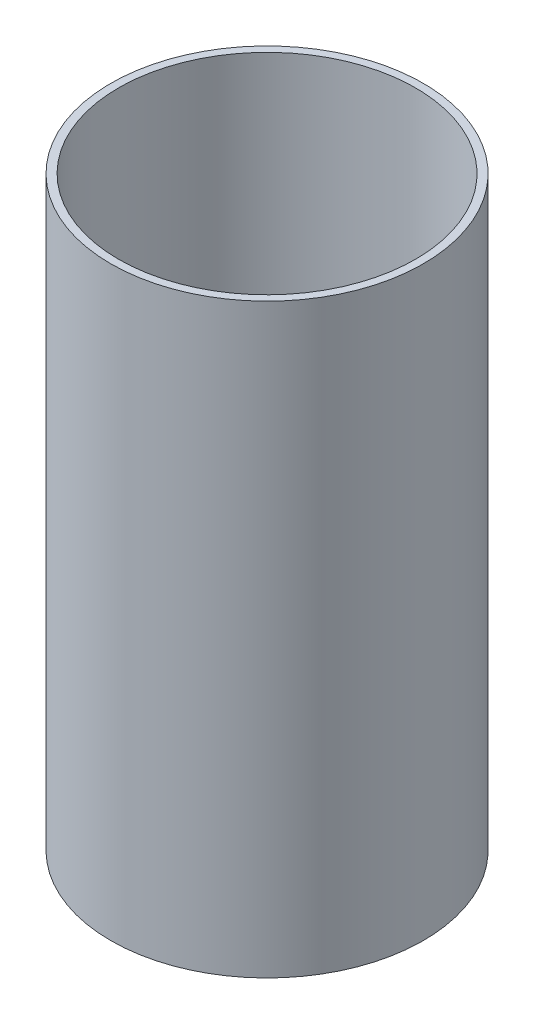
SolidWorks part; units mm, degrees
material "1060 合金"
ref_plane "前视基准面" through (0, 0, 0) normal (0, 0, 1) x (1, 0, 0)
ref_plane "上视基准面" through (0, 0, 0) normal (0, 1, 0) x (1, 0, 0)
ref_plane "右视基准面" through (0, 0, 0) normal (1, 0, 0) x (0, 0, -1)
other "Configuration Table"
sketch "草图1" plane through (0, 0, 0) normal (0, 1, 0) x (1, 0, 0)
  circle A0 centre (0, 0) radius 40
  circle A1 centre (0, 0) radius 38
extrude "凸台-拉伸1" add sketch "草图1" along normal blind 150
